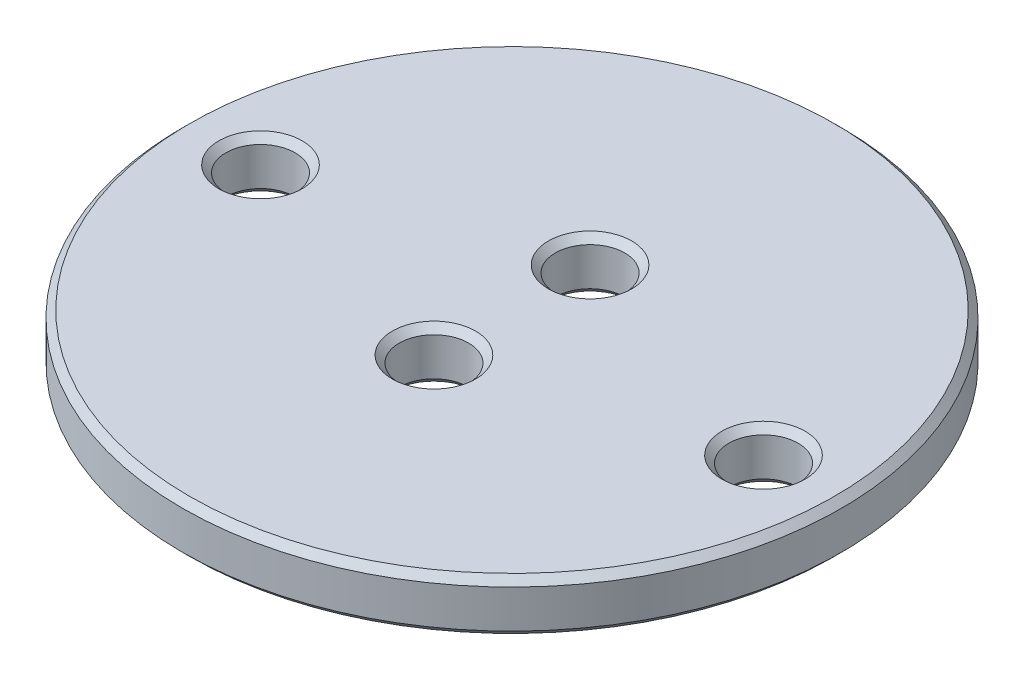
SolidWorks part; units mm, degrees
material "Pine"
ref_plane "Front Plane" through (0, 0, 0) normal (0, 0, 1) x (1, 0, 0)
ref_plane "Top Plane" through (0, 0, 0) normal (0, 1, 0) x (1, 0, 0)
ref_plane "Right Plane" through (0, 0, 0) normal (1, 0, 0) x (0, 0, -1)
sketch "Sketch1" plane through (0, 0, 0) normal (0, 1, 0) x (1, 0, 0)
  line L0 (14.5, 0) -> (-14.5, 0) construction
  line L1 (0, 4.5) -> (0, -4.5) construction
  circle A0 centre (0, 0) radius 19
  circle A1 centre (-14.5, 0) radius 2
  circle A2 centre (14.5, 0) radius 2
  circle A3 centre (0, 4.5) radius 2
  circle A4 centre (0, -4.5) radius 2
  point P7 (0, 0)
  point P12 (0, 0)
  dimension "D1" = 38
  dimension "D2" = 4
  dimension "D3" = 29
  dimension "D4" = 9
extrude "Boss-Extrude1" add sketch "Sketch1" along normal blind 3
chamfer "Chamfer1" distance 0.4 angle 45 10 edges at (0, 0, 6.5) (0, 0, -2.5) (14.5, 0, 2) (-14.5, 0, 2) (0, 0, 19) (0, 3, 6.5) (14.5, 3, 2) (0, 3, 19) (-14.5, 3, 2) (0, 3, -2.5)
